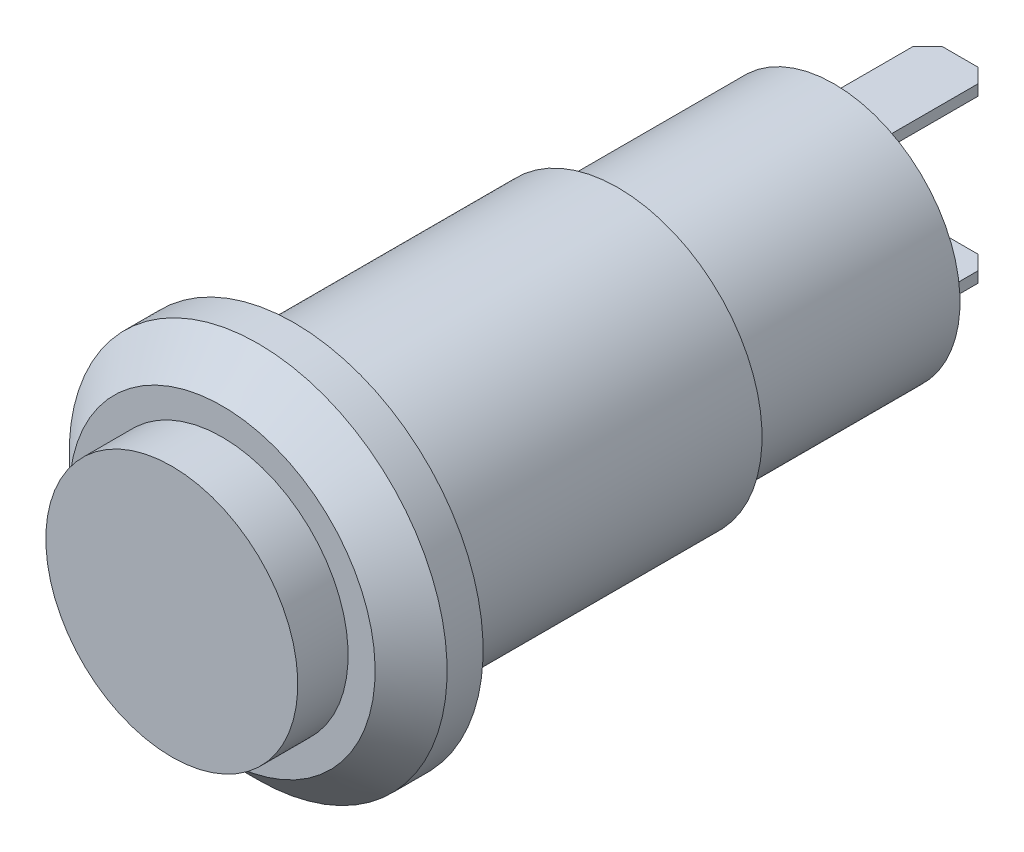
SolidWorks part; units mm, degrees
ref_plane "前视基准面" through (0, 0, 0) normal (0, 0, 1) x (1, 0, 0)
ref_plane "上视基准面" through (0, 0, 0) normal (0, 1, 0) x (1, 0, 0)
ref_plane "右视基准面" through (0, 0, 0) normal (1, 0, 0) x (0, 0, -1)
other "Configuration Table"
sketch "草图1" plane through (0, 0, 0) normal (1, 0, 0) x (0, 0, -1)
  line L0 (0, 0) -> (-18.4, 0) construction
  line L1 (-18.4, 0) -> (-18.4, 3.5)
  line L2 (-18.4, 3.5) -> (-17, 3.5)
  line L3 (-17, 3.5) -> (-17, 5.25)
  line L4 (0, 0) -> (-18.4, 0)
  line L5 (-17, 5.25) -> (-15, 5.25)
  line L6 (-15, 5.25) -> (-15, 4)
  line L7 (-15, 4) -> (-6, 4)
  line L8 (-6, 4) -> (-6, 3.5)
  line L9 (-6, 3.5) -> (0, 3.5)
  line L10 (0, 3.5) -> (0, 0)
  point P4 (-17, 4.375)
  point P13 (-16.5352, 5.25)
  point P14 (0, 0)
  dimension "D1" = 7
  dimension "D2" = 10.5
  dimension "D3" = 2
  dimension "D4" = 8
  dimension "D5" = 7
  dimension "D6" = 18.4
  dimension "D7" = 1.4
  dimension "D8" = 9
revolve "旋转2" add sketch "草图1" angle 360 about L0
cosmetic thread "装饰螺纹线1" parameters "D2"=6.647
sketch "草图6" plane through (0, 0, 0) normal (0, 0, -1) x (-1, 0, 0)
  line L0 (0, 2.3238) -> (0, -2.4276) construction
  line L1 (-2.5808, 0) -> (2.5893, 0) construction
  line L3 (-0.9, 2.1) -> (0.9, 2.1)
  line L4 (-0.9, 2.1) -> (-0.9, 2.4)
  line L5 (-0.9, 2.4) -> (0.9, 2.4)
  line L6 (0.9, 2.1) -> (0.9, 2.4)
  line L7 (0, 2.4) -> (0, 2.1) construction
  line L8 (-0.9, 2.25) -> (0.9, 2.25) construction
  line L9 (-0.9, -2.4) -> (0.9, -2.4)
  line L10 (-0.9, -2.4) -> (-0.9, -2.1)
  line L11 (-0.9, -2.1) -> (0.9, -2.1)
  line L12 (0.9, -2.4) -> (0.9, -2.1)
  line L13 (0, -2.1) -> (0, -2.4) construction
  line L14 (-0.9, -2.25) -> (0.9, -2.25) construction
  point P5 (0, 2.25)
  point P9 (0, -2.25)
  dimension "D1" = 0.3
  dimension "D2" = 1.8
  dimension "D3" = 4.8
extrude "凸台-拉伸2" add sketch "草图6" along normal blind 3.5
chamfer "倒角2" distance 1 angle 45 1 edges at (0, 5.25, 17)
chamfer "倒角3" distance 0.4 angle 45 4 edges at (-0.9, 2.25, -3.5) (-0.9, -2.25, -3.5) (0.9, 2.25, -3.5) (0.9, -2.25, -3.5)
